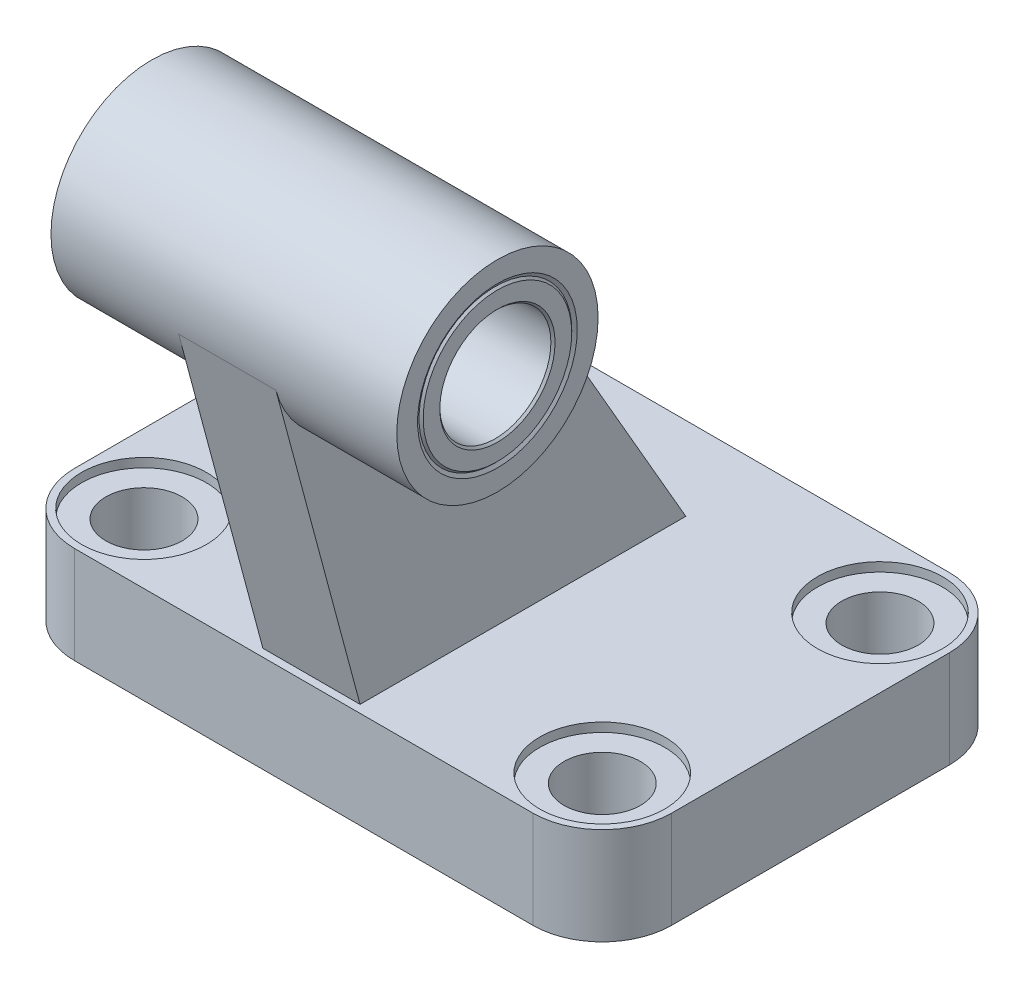
SolidWorks part; units mm, degrees
ref_plane "Front Plane" through (0, 0, 0) normal (0, 0, 1) x (1, 0, 0)
ref_plane "Top Plane" through (0, 0, 0) normal (0, 1, 0) x (1, 0, 0)
ref_plane "Right Plane" through (0, 0, 0) normal (1, 0, 0) x (0, 0, -1)
ref_plane "Plane1" through (0, 0, 0) normal (0, 1, 0) x (1, 0, 0)
sketch "Sketch1" plane through (0, 0, 0) normal (0, 1, 0) x (1, 0, 0)
  line L0 (-33, -30) -> (33, -30)
  line L1 (43, -20) -> (43, 20)
  line L2 (33, 30) -> (-33, 30)
  line L3 (-43, 20) -> (-43, -20)
  arc A0 (-43, -20) -> (-33, -30) centre (-33, -20) ccw
  arc A1 (33, -30) -> (43, -20) centre (33, -20) ccw
  arc A2 (43, 20) -> (33, 30) centre (33, 20) ccw
  arc A3 (-33, 30) -> (-43, 20) centre (-33, 20) ccw
extrude "Boss-Extrude1" add sketch "Sketch1" along normal blind 14
ref_plane "Plane2" through (0, 0, 0) normal (1, 0, 0) x (0, 0, -1)
sketch "Sketch2" plane through (0, 0, 0) normal (1, 0, 0) x (0, 0, -1)
  line L0 (-41.0059, 59.2471) -> (-28.882, 14)
  line L1 (-28.882, 14) -> (18.0333, 14)
  line L2 (18.0333, 14) -> (-14.4426, 70.25)
  line L3 (-14.4426, 70.25) -> (-41.0059, 59.2471)
extrude "Boss-Extrude2" add sketch "Sketch2" against normal blind 7 and the other way blind 7
ref_plane "Plane3" through (0, 0, 0) normal (1, 0, 0) x (0, 0, -1)
sketch "Sketch3" plane through (0, 0, 0) normal (1, 0, 0) x (0, 0, -1)
  circle A0 centre (-27, 63) radius 14.5
extrude "Boss-Extrude3" add sketch "Sketch3" against normal blind 24.9 and the other way blind 24.9
ref_plane "Plane4" through (0, 0, 20) normal (0, 0, 1) x (1, 0, 0)
sketch "Sketch4" plane through (0, 0, 20) normal (0, 0, 1) x (1, 0, 0)
  line L0 (-33, 0) -> (-38.5, 0)
  line L1 (-38.5, 0) -> (-38.5, 12.7)
  line L2 (-38.5, 12.7) -> (-42, 12.7)
  line L3 (-42, 12.7) -> (-42, 14)
  line L4 (-42, 14) -> (-33, 14)
  line L5 (-33, 14) -> (-33, 0)
  line L6 (-33, 14) -> (-33, 0) construction
revolve "Cut-Revolve1" cut sketch "Sketch4" angle 360 about L6
ref_plane "Plane5" through (0, 0, -20) normal (0, 0, 1) x (1, 0, 0)
sketch "Sketch5" plane through (0, 0, -20) normal (0, 0, 1) x (1, 0, 0)
  line L0 (-33, 0) -> (-38.5, 0)
  line L1 (-38.5, 0) -> (-38.5, 12.7)
  line L2 (-38.5, 12.7) -> (-42, 12.7)
  line L3 (-42, 12.7) -> (-42, 14)
  line L4 (-42, 14) -> (-33, 14)
  line L5 (-33, 14) -> (-33, 0)
  line L6 (-33, 14) -> (-33, 0) construction
revolve "Cut-Revolve2" cut sketch "Sketch5" angle 360 about L6
ref_plane "Plane6" through (0, 0, 20) normal (0, 0, 1) x (1, 0, 0)
sketch "Sketch6" plane through (0, 0, 20) normal (0, 0, 1) x (1, 0, 0)
  line L0 (33, 0) -> (27.5, 0)
  line L1 (27.5, 0) -> (27.5, 12.7)
  line L2 (27.5, 12.7) -> (24, 12.7)
  line L3 (24, 12.7) -> (24, 14)
  line L4 (24, 14) -> (33, 14)
  line L5 (33, 14) -> (33, 0)
  line L6 (33, 14) -> (33, 0) construction
revolve "Cut-Revolve3" cut sketch "Sketch6" angle 360 about L6
ref_plane "Plane7" through (0, 0, -20) normal (0, 0, 1) x (1, 0, 0)
sketch "Sketch7" plane through (0, 0, -20) normal (0, 0, 1) x (1, 0, 0)
  line L0 (33, 0) -> (27.5, 0)
  line L1 (27.5, 0) -> (27.5, 12.7)
  line L2 (27.5, 12.7) -> (24, 12.7)
  line L3 (24, 12.7) -> (24, 14)
  line L4 (24, 14) -> (33, 14)
  line L5 (33, 14) -> (33, 0)
  line L6 (33, 14) -> (33, 0) construction
revolve "Cut-Revolve4" cut sketch "Sketch7" angle 360 about L6
ref_plane "Plane8" through (0, 0, 27) normal (0, 0, 1) x (1, 0, 0)
sketch "Sketch8" plane through (0, 0, 27) normal (0, 0, 1) x (1, 0, 0)
  line L0 (-24.9, 63) -> (-24.9, 74.5)
  line L1 (-24.9, 74.5) -> (-24.6113, 74)
  line L2 (-24.6113, 74) -> (24.6113, 74)
  line L3 (24.6113, 74) -> (24.9, 74.5)
  line L4 (24.9, 74.5) -> (24.9, 63)
  line L5 (24.9, 63) -> (-24.9, 63)
  line L6 (24.9, 63) -> (-24.9, 63) construction
revolve "Cut-Revolve5" cut sketch "Sketch8" angle 360 about L6
ref_plane "Plane9" through (0, 0, 27) normal (0, 0, 1) x (1, 0, 0)
sketch "Sketch9" plane through (0, 0, 27) normal (0, 0, 1) x (1, 0, 0)
  line L0 (-24.9, 71.3) -> (-24.6, 71)
  line L1 (-24.6, 71) -> (24.6, 71)
  line L2 (24.6, 71) -> (24.9, 71.3)
  line L3 (24.9, 71.3) -> (24.9, 73.7)
  line L4 (24.9, 73.7) -> (24.6, 74)
  line L5 (24.6, 74) -> (-24.6, 74)
  line L6 (-24.6, 74) -> (-24.9, 73.7)
  line L7 (-24.9, 73.7) -> (-24.9, 71.3)
  line L8 (24.9, 63) -> (-24.9, 63) construction
revolve "Revolve1" add sketch "Sketch9" angle 360 about L8
